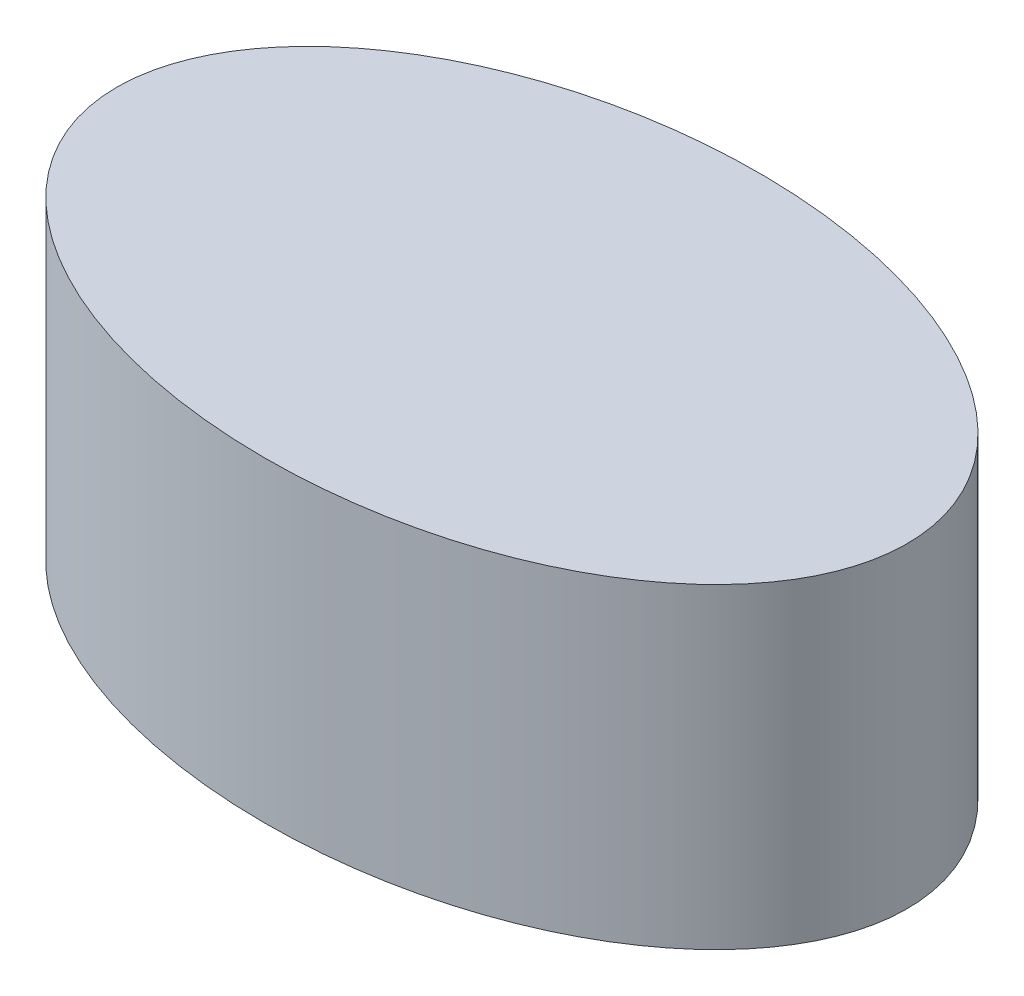
SolidWorks part; units mm, degrees
ref_plane "Front Plane" through (0, 0, 0) normal (0, 0, 1) x (1, 0, 0)
ref_plane "Top Plane" through (0, 0, 0) normal (0, 1, 0) x (1, 0, 0)
ref_plane "Right Plane" through (0, 0, 0) normal (1, 0, 0) x (0, 0, -1)
sketch "Leather_belt" plane through (0, 0, 0) normal (0, 1, 0) x (1, 0, 0)
  ellipse E0 centre (0, 0) end of major axis (-200, 0) minor radius 125
  dimension "D1" = 250
  dimension "D2" = 400
extrude "Boss-Extrude1" add sketch "Leather_belt" along normal blind 160
equation "\"waist_length\"= 400"
equation "\"waist_width\"= 250"
equation "\"D1@Leather_belt\"=\"waist_width\""
equation "\"D2@Leather_belt\"=\"waist_length\""
